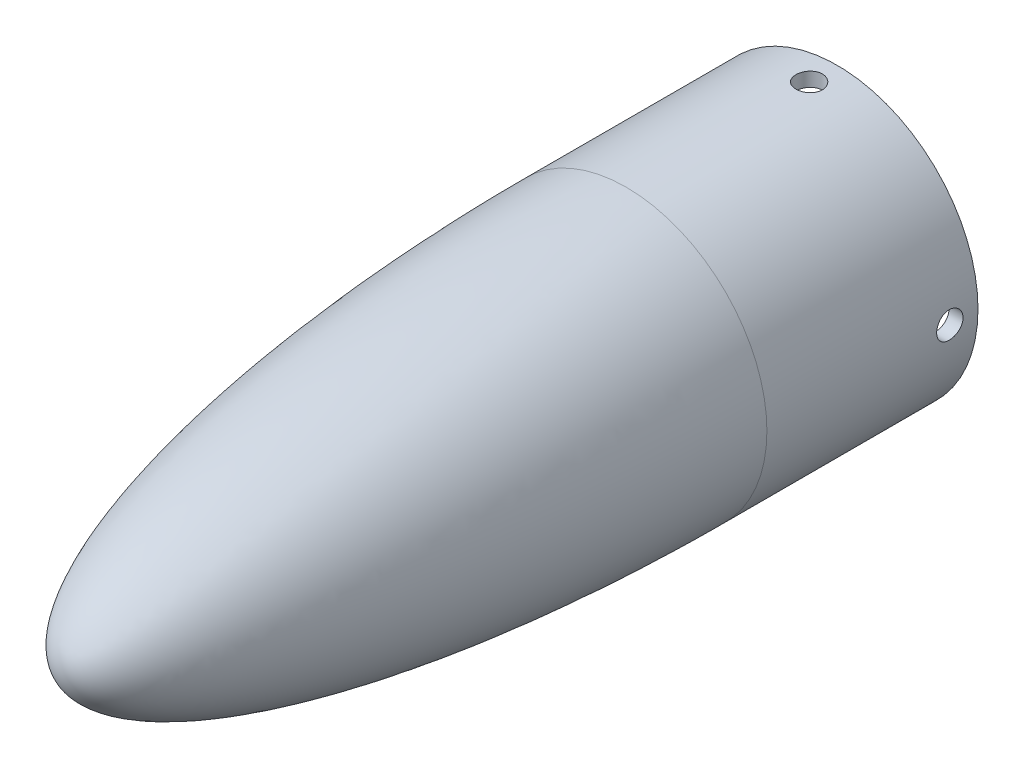
SolidWorks part; units mm, degrees
material "PET"
ref_plane "Front Plane" through (0, 0, 0) normal (0, 0, 1) x (1, 0, 0)
ref_plane "Top Plane" through (0, 0, 0) normal (0, 1, 0) x (1, 0, 0)
ref_plane "Right Plane" through (0, 0, 0) normal (1, 0, 0) x (0, 0, -1)
sketch "Sketch2" plane through (0, 0, 0) normal (1, 0, 0) x (0, 0, -1)
  line L0 (0, 0) -> (26379.123, 0) construction
  line L2 (0, 20) -> (30, 20)
  line L5 (30, 20) -> (30, 0)
  line L6 (28, 18) -> (28, 0)
  line L7 (0, 18) -> (28, 18)
  line L8 (-80, 0) -> (30, 0)
  line L10 (-77.5893, 1.5945) -> (28, -17.6036) construction
  line L11 (-80, 0) -> (30, -20) construction
  line L12 (28, 18) -> (28, -17.6036) construction
  line L13 (30, 20) -> (30, -20) construction
  ellipse E0 centre (0, 0) end of major axis (-80, 0) minor radius 20 (0, 20) -> (-80, 0) ccw
  spline S0 degree 1 poles (0, 18) (-77.5893, 1.5945) knots 0 0 1 1 construction
  spline S1 degree 3 poles (0, 18) (-2.3915, 18) (-7.1855, 17.9459) (-16.6826, 17.622) (-28.2601, 16.8176) (-41.2126, 15.2456) (-52.7914, 13.123) (-60.963, 10.9609) (-66.4363, 9.0512) (-69.9686, 7.5485) (-72.8895, 6.0002) (-74.7831, 4.7028) (-75.9614, 3.688) (-76.6743, 2.9526) (-77.227, 2.2381) (-77.4745, 1.8229) (-77.5893, 1.5945) knots -1.570796 -1.570796 -1.570796 -1.570796 -1.48043 -1.390064 -1.209332 -1.0286 -0.847868 -0.667136 -0.57677 -0.486404 -0.396038 -0.305672 -0.260489 -0.215306 -0.170123 -0.124939 -0.124939 -0.124939 -0.124939 only from (0, 18) to (-78, 0)
  dimension "D1" = 80
  dimension "D2" = 20
  dimension "D3" = 30
revolve "Revolve1" add sketch "Sketch2" angle 360 about L0
shell "Shell1" thickness 2
ref_plane "Plane1" through (20, 0, 0) normal (1, 0, 0) x (0, 0, -1)
sketch "Sketch3" plane through (20, 0, 0) normal (1, 0, 0) x (0, 0, -1)
  line L0 (30, -20) -> (30, 20) construction
  circle A0 centre (26, 0) radius 1.875
  dimension "D2" = 3.75
  dimension "D1" = 4
extrude "Cut-Extrude1" cut sketch "Sketch3" against normal up to next
pattern_circular "CirPattern1" count 4 over 360 about axis through (0, 0, -30) along (0, 0, 1) of "Cut-Extrude1"
